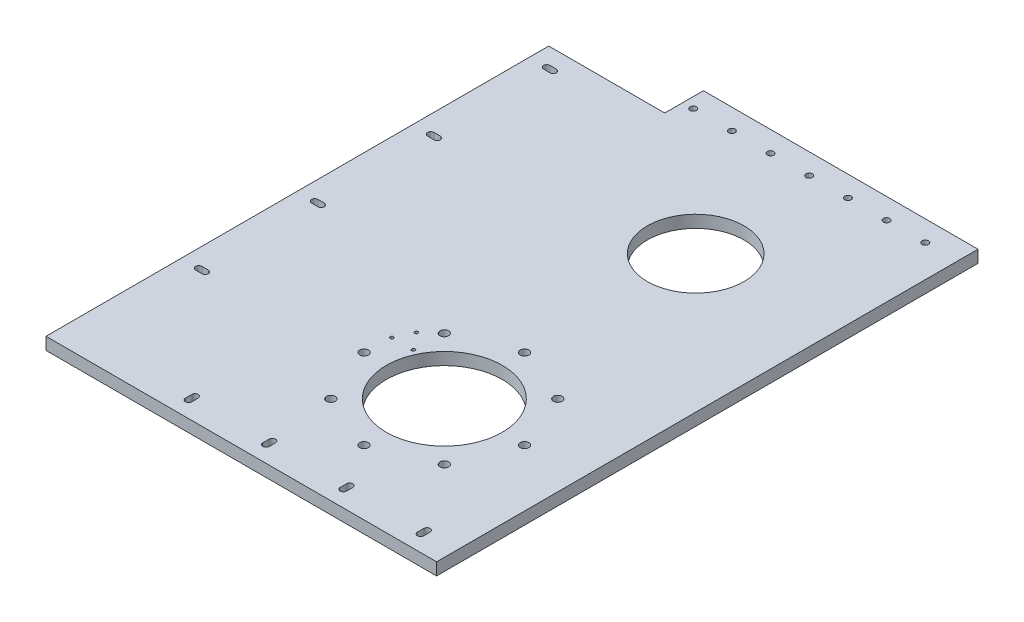
SolidWorks part; units mm, degrees
ref_plane "Front Plane" through (0, 0, 0) normal (0, 0, 1) x (1, 0, 0)
ref_plane "Top Plane" through (0, 0, 0) normal (0, 1, 0) x (1, 0, 0)
ref_plane "Right Plane" through (0, 0, 0) normal (1, 0, 0) x (0, 0, -1)
sketch "Sketch1" plane through (0, 0, 0) normal (0, 1, 0) x (1, 0, 0)
  line L3 (-71, 140) -> (71, 140)
  line L4 (71, -140) -> (71, 140)
  line L5 (0, 140) -> (0, -135) construction
  line L6 (0, 0) -> (71, 0) construction
  line L10 (-71, 140) -> (-71, 120)
  line L11 (-71, 120) -> (-131, 120)
  line L12 (-131, 120) -> (-131, -140)
  line L13 (-131, -140) -> (71, -140)
  point P0 (0, 0)
  dimension "D1" = 280
  dimension "D2" = 20
  dimension "D3" = 202
  dimension "D4" = 60
extrude "Boss-Extrude1" add sketch "Sketch1" along normal blind 6.35
sketch "Sketch2" plane through (0, 6.35, 0) normal (0, 1, 0) x (1, 0, 0)
  line L1 (0, 140) -> (0, -140) construction
  line L2 (71, 140) -> (-71, 140) construction
  line L3 (-131, -140) -> (71, -140) construction
  circle A0 centre (0, -65) radius 41.5 construction
  circle A1 centre (0, -23.5) radius 2.25
  circle A2 centre (29.3449, -35.6551) radius 2.25
  circle A3 centre (41.5, -65) radius 2.25
  circle A4 centre (29.3449, -94.3449) radius 2.25
  circle A5 centre (0, -106.5) radius 2.25
  circle A6 centre (-29.3449, -94.3449) radius 2.25
  circle A7 centre (-41.5, -65) radius 2.25
  circle A8 centre (-29.3449, -35.6551) radius 2.25
  circle A9 centre (0, -65) radius 80 construction
  circle A10 centre (0, -65) radius 30
  point P22 (0, -65)
  dimension "D1" = 83
  dimension "D2" = 4.5
  dimension "D4" = 160
  dimension "D6" = 60
  dimension "D5" = 75
  dimension "D3" = 8
extrude "Cut-Extrude1" cut sketch "Sketch2" against normal through all
sketch "Sketch6" plane through (0, 6.35, 0) normal (0, 1, 0) x (1, 0, 0)
  line L0 (0, -65) -> (-38.9712, -46.8274) construction
  line L1 (0, -65) -> (0, -23.5) construction
  line L2 (-40.9787, -51.1324) -> (-36.9638, -42.5225) construction
  line L3 (-36.9638, -42.5225) -> (-27.9007, -46.7486) construction
  circle A0 centre (0, -65) radius 30 construction
  circle A1 centre (-36.9638, -42.5225) radius 0.85
  circle A2 centre (-40.9787, -51.1324) radius 0.85
  circle A5 centre (-29.9082, -51.0536) radius 0.85
  point P7 (-38.9712, -46.8274)
  dimension "D4" = 1.7
  dimension "D5" = 10
  dimension "D7" = 10
  dimension "D6" = 1.7
  dimension "D1" = 43
  dimension "D2" = 9.5
  dimension "D3" = 65
extrude "Cut-Extrude5" cut sketch "Sketch6" against normal through all
sketch "Sketch8" plane through (0, 6.35, 0) normal (0, 1, 0) x (1, 0, 0)
  line L1 (71, 140) -> (-71, 140) construction
  line L2 (65, -20.6305) -> (65, 140) construction
  line L3 (71, -140) -> (71, 140) construction
  line L5 (45, 41.8036) -> (45, 140) construction
  circle A0 centre (0, 65) radius 25
  circle A1 centre (0, -65) radius 30 construction
  dimension "D1" = 130
  dimension "D2" = 50
  dimension "D3" = 6
  dimension "D4" = 20
extrude "Cut-Extrude9" cut sketch "Sketch8" against normal through all
sketch "Sketch9" plane through (0, 0, 0) normal (0, -1, 0) x (-1, 0, 0)
  circle A1 centre (45.6, 129.325) radius 1.65
  circle A2 centre (5.6, 129.325) radius 1.65
  circle A3 centre (-34.4, 129.325) radius 1.65
  circle A4 centre (65.6, 129.325) radius 1.65
  circle A5 centre (25.6, 129.325) radius 1.65
  circle A6 centre (-14.4, 129.325) radius 1.65
  circle A7 centre (-54.4, 129.325) radius 1.65
extrude "Cut-Extrude10" cut sketch "Sketch9" against normal blind 30
sketch "Sketch10" plane through (0, 0, 0) normal (0, -1, 0) x (1, 0, 0)
  line L0 (-121.975, 10) -> (-118.675, 10) construction
  line L3 (-121.975, 11.65) -> (-118.675, 11.65)
  line L4 (-121.975, 8.35) -> (-118.675, 8.35)
  line L5 (-121.975, 70) -> (-118.675, 70) construction
  line L6 (-121.975, 71.65) -> (-118.675, 71.65)
  line L7 (-121.975, 68.35) -> (-118.675, 68.35)
  line L8 (-121.975, -50) -> (-118.675, -50) construction
  line L9 (-121.975, -48.35) -> (-118.675, -48.35)
  line L10 (-121.975, -51.65) -> (-118.675, -51.65)
  line L11 (-121.975, -110) -> (-118.675, -110) construction
  line L12 (-121.975, -108.35) -> (-118.675, -108.35)
  line L13 (-121.975, -111.65) -> (-118.675, -111.65)
  circle A0 centre (-120.325, -110) radius 1.65
  circle A1 centre (-120.325, -50) radius 1.65
  circle A2 centre (-120.325, 10) radius 1.65
  circle A3 centre (-120.325, 70) radius 1.65
  arc A6 (-121.975, 11.65) -> (-121.975, 8.35) centre (-121.975, 10) ccw
  arc A7 (-118.675, 8.35) -> (-118.675, 11.65) centre (-118.675, 10) ccw
  arc A8 (-121.975, 71.65) -> (-121.975, 68.35) centre (-121.975, 70) ccw
  arc A9 (-118.675, 68.35) -> (-118.675, 71.65) centre (-118.675, 70) ccw
  arc A10 (-121.975, -48.35) -> (-121.975, -51.65) centre (-121.975, -50) ccw
  arc A11 (-118.675, -51.65) -> (-118.675, -48.35) centre (-118.675, -50) ccw
  arc A12 (-121.975, -108.35) -> (-121.975, -111.65) centre (-121.975, -110) ccw
  arc A13 (-118.675, -111.65) -> (-118.675, -108.35) centre (-118.675, -110) ccw
  point P14 (-120.325, 10)
  point P21 (-120.325, 70)
  point P28 (-120.325, -50)
  point P35 (-120.325, -110)
  dimension "D1" = 3.3
  dimension "D2" = 3.3
  dimension "D3" = 3.3
  dimension "D4" = 3.3
  dimension "D5" = 1.65
  dimension "D6" = 1.65
  dimension "D7" = 1.65
  dimension "D8" = 1.65
sketch "Sketch11" plane through (0, 6.35, 0) normal (0, 1, 0) x (1, 0, 0)
  line L0 (71, -127.15) -> (-131, -127.15) construction
  line L1 (71, -140) -> (71, 140) construction
  line L2 (456.625, -127.15) -> (-127.825, -127.15) construction
  line L3 (-131, 120) -> (-131, -140) construction
  line L4 (71, -132.85) -> (-131, -132.85) construction
  line L5 (456.625, -132.85) -> (-127.825, -132.85) construction
  line L6 (-65.6, 129.325) -> (-65.6, -130.005) construction
  line L7 (-65.6, -130.005) -> (71, -130) construction
  line L8 (456.625, -130) -> (-127.825, -130) construction
  line L9 (-25.6, 129.325) -> (-25.6, -130.0035) construction
  line L10 (14.4, 129.325) -> (14.4, -130.0021) construction
  line L11 (54.4, 129.325) -> (54.4, -130.0006) construction
  line L12 (-65.6, -128.355) -> (-65.6, -131.655) construction
  line L13 (-63.95, -128.355) -> (-63.95, -131.655)
  line L14 (-67.25, -128.355) -> (-67.25, -131.655)
  line L15 (-25.6, -128.3535) -> (-25.6, -131.6535) construction
  line L16 (-23.95, -128.3535) -> (-23.95, -131.6535)
  line L17 (-27.25, -128.3535) -> (-27.25, -131.6535)
  line L18 (14.4, -128.3521) -> (14.4, -131.6521) construction
  line L19 (16.05, -128.3521) -> (16.05, -131.6521)
  line L20 (12.75, -128.3521) -> (12.75, -131.6521)
  line L21 (54.4, -128.3506) -> (54.4, -131.6506) construction
  line L22 (56.05, -128.3506) -> (56.05, -131.6506)
  line L23 (52.75, -128.3506) -> (52.75, -131.6506)
  circle A0 centre (-65.6, -130.005) radius 1.65 construction
  circle A1 centre (-25.6, -130.0035) radius 1.65 construction
  circle A2 centre (14.4, -130.0021) radius 1.65 construction
  circle A3 centre (54.4, -130.0006) radius 1.65 construction
  arc A4 (-63.95, -128.355) -> (-67.25, -128.355) centre (-65.6, -128.355) ccw
  arc A5 (-67.25, -131.655) -> (-63.95, -131.655) centre (-65.6, -131.655) ccw
  arc A6 (-23.95, -128.3535) -> (-27.25, -128.3535) centre (-25.6, -128.3535) ccw
  arc A7 (-27.25, -131.6535) -> (-23.95, -131.6535) centre (-25.6, -131.6535) ccw
  arc A8 (16.05, -128.3521) -> (12.75, -128.3521) centre (14.4, -128.3521) ccw
  arc A9 (12.75, -131.6521) -> (16.05, -131.6521) centre (14.4, -131.6521) ccw
  arc A10 (56.05, -128.3506) -> (52.75, -128.3506) centre (54.4, -128.3506) ccw
  arc A11 (52.75, -131.6506) -> (56.05, -131.6506) centre (54.4, -131.6506) ccw
  point P33 (-65.6, -130.005)
  point P39 (-25.6, -130.0035)
  point P46 (14.4, -130.0021)
  point P53 (54.4, -130.0006)
  dimension "D2" = 3.3
  dimension "D1" = 259.33
extrude "Cut-Extrude12" cut sketch "Sketch11" against normal blind 30
extrude "Cut-Extrude13" cut sketch "Sketch10" against normal blind 10 contours A0 | L13 A13 L12 A0 | L12 A12 L13 A0 | L9 A10 L10 A1 | A1 | L10 A11 L9 A1 | L3 A6 L4 A2 | A2 | L4 A7 L3 A2 | L6 A8 L7 A3 | A3 | L7 A9 L6 A3
